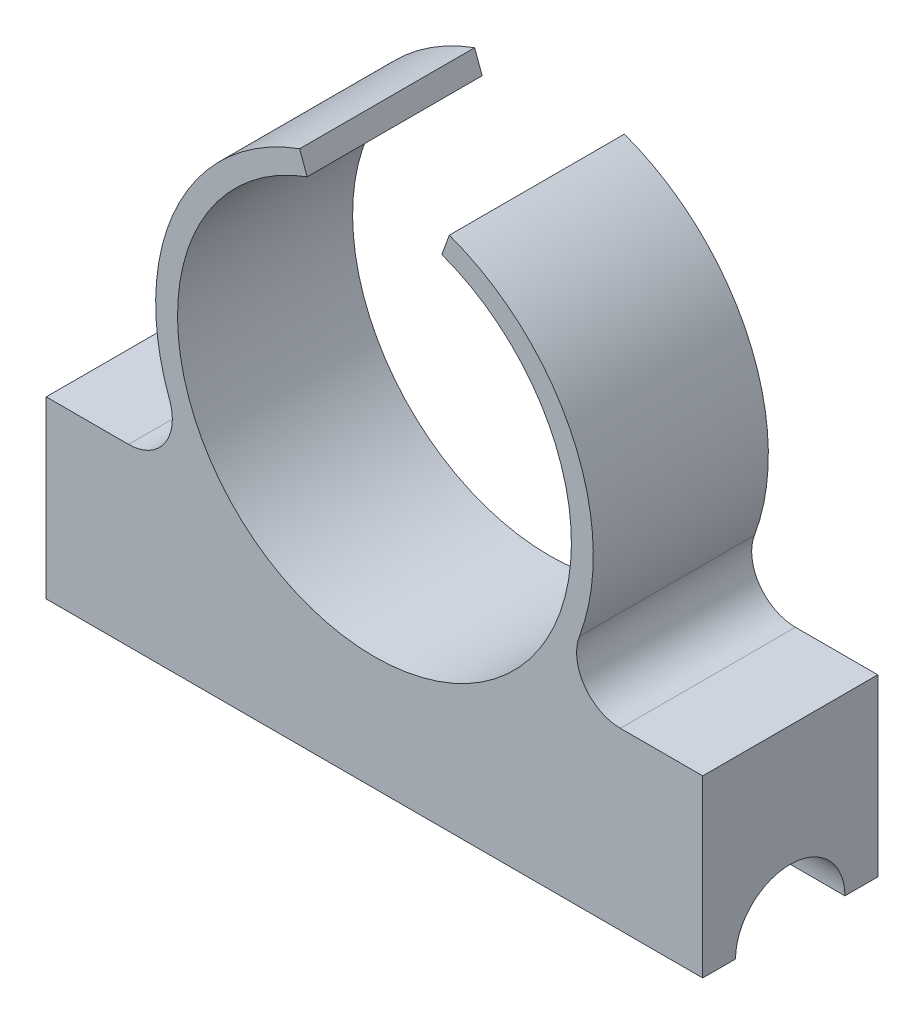
SolidWorks part; units mm, degrees
ref_plane "Front Plane" through (0, 0, 0) normal (0, 0, 1) x (1, 0, 0)
ref_plane "Top Plane" through (0, 0, 0) normal (0, 1, 0) x (1, 0, 0)
ref_plane "Right Plane" through (0, 0, 0) normal (1, 0, 0) x (0, 0, -1)
sketch "Sketch1" plane through (0, 0, 0) normal (0, 0, 1) x (1, 0, 0)
  line L0 (3.8901, 2.5) -> (15, 2.5)
  line L1 (-15, -2.5) -> (15, -2.5)
  line L2 (-15, -2.5) -> (-15, 2.5)
  line L3 (-15, 2.5) -> (-3.8901, 2.5)
  line L4 (15, -2.5) -> (15, 2.5)
  arc A3 (3.8901, 2.5) -> (-3.8901, 2.5) centre (0, 11.7123) ccw
  point P0 (0, 0)
extrude "Boss-Extrude1" add sketch "Sketch1" along normal blind 8
sketch "Sketch2" plane through (0, 0, 8) normal (0, 0, 1) x (1, 0, 0)
  circle A0 centre (0, 11.7123) radius 9
extrude "Cut-Extrude1" cut sketch "Sketch2" against normal blind 35
sketch "Sketch3" plane through (0, 0, 0) normal (0, 0, -1) x (-1, 0, 0)
  line L1 (-0.25, 22.4592) -> (0.25, 22.4592)
  line L2 (-0.25, 22.4592) -> (-0.25, 20.5838)
  line L3 (-0.25, 20.5838) -> (0.25, 20.5838)
  line L4 (0.25, 22.4592) -> (0.25, 20.5838)
  line L5 (-0.25, 22.4592) -> (0.25, 20.5838) construction
  line L6 (-0.25, 20.5838) -> (0.25, 22.4592) construction
  point P0 (0, 21.5215)
extrude "Cut-Extrude2" cut sketch "Sketch3" against normal blind 25
sketch "Sketch4" plane through (15, 0, 0) normal (1, 0, 0) x (0, 0, -1)
  line L0 (-8, -2.5) -> (0, -2.5) construction
  circle A0 centre (-4, -2.5) radius 2.5
extrude "Cut-Extrude3" cut sketch "Sketch4" against normal blind 110
sketch "Sketch6" plane through (0, 0, 8) normal (0, 0, 1) x (1, 0, 0)
  line L1 (-2.5, 26.3053) -> (2.5, 26.3053)
  line L2 (-2.5, 26.3053) -> (-2.5, 19.1581)
  line L3 (-2.5, 19.1581) -> (2.5, 19.1581)
  line L4 (2.5, 26.3053) -> (2.5, 19.1581)
  line L5 (-2.5, 26.3053) -> (2.5, 19.1581) construction
  line L6 (-2.5, 19.1581) -> (2.5, 26.3053) construction
  point P0 (0, 22.7317)
extrude "Cut-Extrude4" cut sketch "Sketch6" against normal blind 10
fillet "Fillet1" radius 0.5 2 edges at (3.8901, 2.5, 4) (-3.8901, 2.5, 4)
sketch "Sketch8" plane through (-15, 0, 0) normal (-1, 0, 0) x (0, 0, 1)
  line L5 (0, 2.5) -> (8, 2.5)
  line L6 (0, 2.5) -> (0, 5.5)
  line L7 (0, 5.5) -> (8, 5.5)
  line L8 (8, 2.5) -> (8, 5.5)
  point P0 (0, 2.5)
extrude "Boss-Extrude2" add sketch "Sketch8" against normal blind 30
sketch "Sketch9" plane through (0, 0, 0) normal (0, 0, -1) x (-1, 0, 0)
  circle A0 centre (0, 11.7123) radius 9
extrude "Cut-Extrude5" cut sketch "Sketch9" against normal blind 30
fillet "Fillet2" radius 2 2 edges at (7.8362, 5.5, 4) (-7.8362, 5.5, 4)
sketch "Sketch10" plane through (0, 0, 0) normal (0, 0, -1) x (-1, 0, 0)
  line L0 (0, 11.7123) -> (3.4202, 21.1093)
  line L2 (0, 11.7123) -> (-3.4202, 21.1093)
  arc A0 (9.3636, 8.2021) -> (2.5, 21.3948) centre (0, 11.7123) ccw construction
  arc A1 (-3.4202, 21.1093) -> (3.4202, 21.1093) centre (0, 21.1093) cw
extrude "Cut-Extrude7" cut sketch "Sketch10" against normal blind 30
